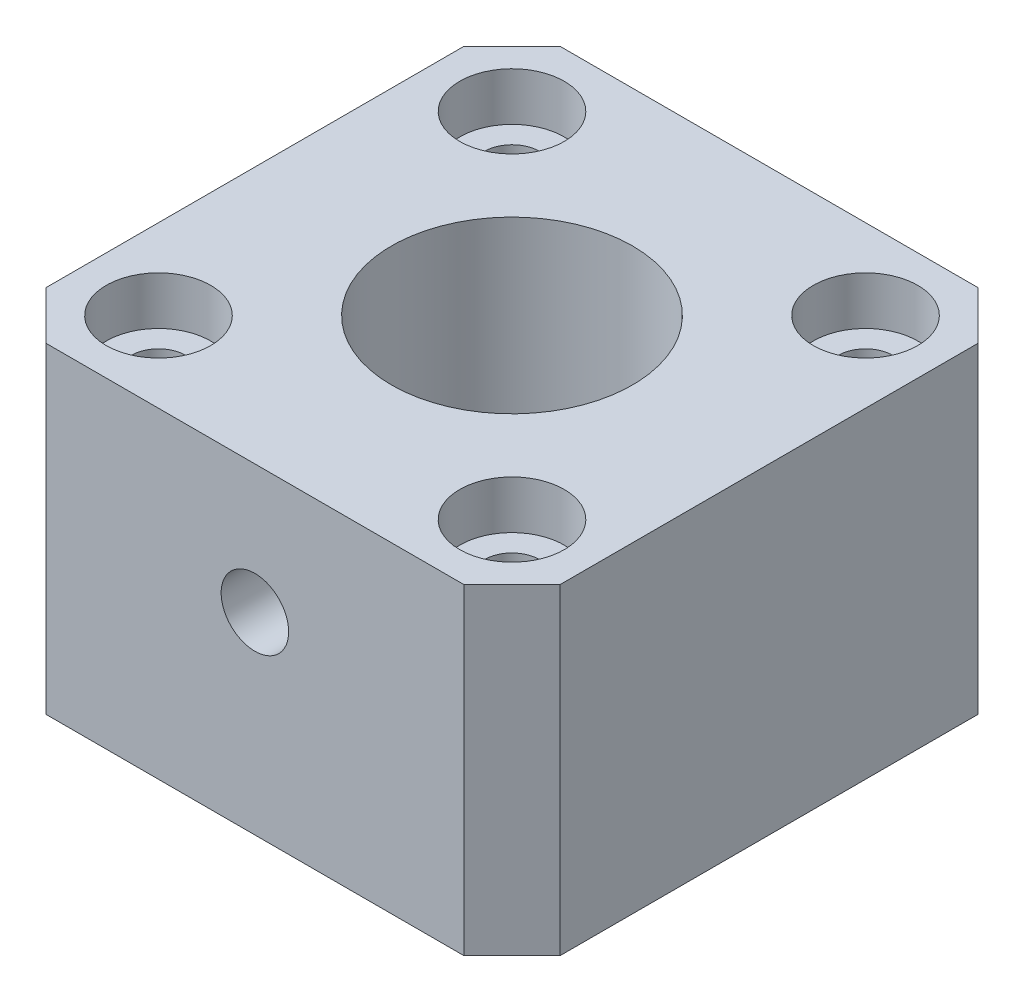
SolidWorks part; units mm, degrees
ref_plane "Front Plane" through (0, 0, 0) normal (0, 0, 1) x (1, 0, 0)
ref_plane "Top Plane" through (0, 0, 0) normal (0, 1, 0) x (1, 0, 0)
ref_plane "Right Plane" through (0, 0, 0) normal (1, 0, 0) x (0, 0, -1)
sketch "Sketch1" plane through (0, 0, 0) normal (0, 1, 0) x (1, 0, 0)
  line L0 (-11, 11) -> (-11, -11) construction
  line L1 (16, -16) -> (-16, -16)
  line L2 (16, -16) -> (16, 16)
  line L3 (16, 16) -> (-16, 16)
  line L4 (-16, -16) -> (-16, 16)
  line L5 (16, -16) -> (-16, 16) construction
  line L6 (16, 16) -> (-16, -16) construction
  line L7 (-11, -11) -> (11, -11) construction
  line L8 (11, -11) -> (11, 11) construction
  line L9 (11, 11) -> (-11, 11) construction
  circle A0 centre (0, 0) radius 7.5
  circle A1 centre (-11, 11) radius 5 construction
  circle A2 centre (-11, 11) radius 1.5 construction
  circle A3 centre (-11, 11) radius 3 construction
  dimension "D1" = 6
  dimension "D2" = 3
  dimension "D3" = 2
  dimension "D4" = 15
  dimension "D5" = 22
extrude "Boss-Extrude1" add sketch "Sketch1" along normal blind 20
hole_wizard "CBORE for M3 SHCS1" positions "Sketch2" profile "Sketch3" counterbore size "M3" standard "ANSI Metric" end condition through all
sketch "Sketch2" plane through (0, 20, 0) normal (0, 1, 0) x (1, 0, 0)
  point P0 (-11, 11)
  point P3 (11, 11)
  point P6 (11, -11)
  point P9 (-11, -11)
sketch "Sketch3" plane through (-11, 20, -11) normal (1, 0, 0) x (0, 0, 1)
  line L0 (0, 0) -> (0, 20)
  line L1 (0, 20) -> (1.7, 20)
  line L3 (1.7, 20) -> (1.7, 3)
  line L4 (1.7, 3) -> (3.25, 3)
  line L5 (3.25, 3) -> (3.25, 0)
  line L7 (3.25, 0) -> (0, 0)
  line L11 (0, -6.35) -> (0, 107.95) construction
  dimension "Thru Hole Dia." = 3.4
  dimension "Thru Hole Depth" = 20
  dimension "C'Bore Dia." = 6.5
  dimension "C'Bore Depth" = 3
sketch "Sketch4" plane through (0, 0, 16) normal (0, 0, 1) x (1, 0, 0)
  line L0 (0, 20) -> (0, 12) construction
  line L1 (-16, 20) -> (16, 20) construction
  dimension "D1" = 8
hole_wizard "M5x0.8 Tapped Hole1" positions "Sketch5" profile "Sketch6" tap size "M5x0.8" standard "ANSI Metric"
sketch "Sketch5" plane through (0, 0, 16) normal (0, 0, 1) x (1, 0, 0)
  point P0 (0, 12)
sketch "Sketch6" plane through (0, 12, 16) normal (1, 0, 0) x (0, -1, 0)
  line L0 (0, 0) -> (0, 8.5)
  line L1 (0, 8.5) -> (2.1, 8.5)
  line L2 (2.1, 8.5) -> (2.1, 0)
  line L5 (2.1, 0) -> (0, 0)
  line L11 (0, -6.35) -> (0, 107.95) construction
  dimension "Thru Tap Drill Dia." = 4.2
  dimension "Thru Tap Drill Depth" = 8.5
cosmetic thread "Hole Thread1" parameters "D2"=5
chamfer "Chamfer1" distance 3 angle 45 4 edges at (16, 10, 16) (-16, 10, 16) (16, 10, -16) (-16, 10, -16)
